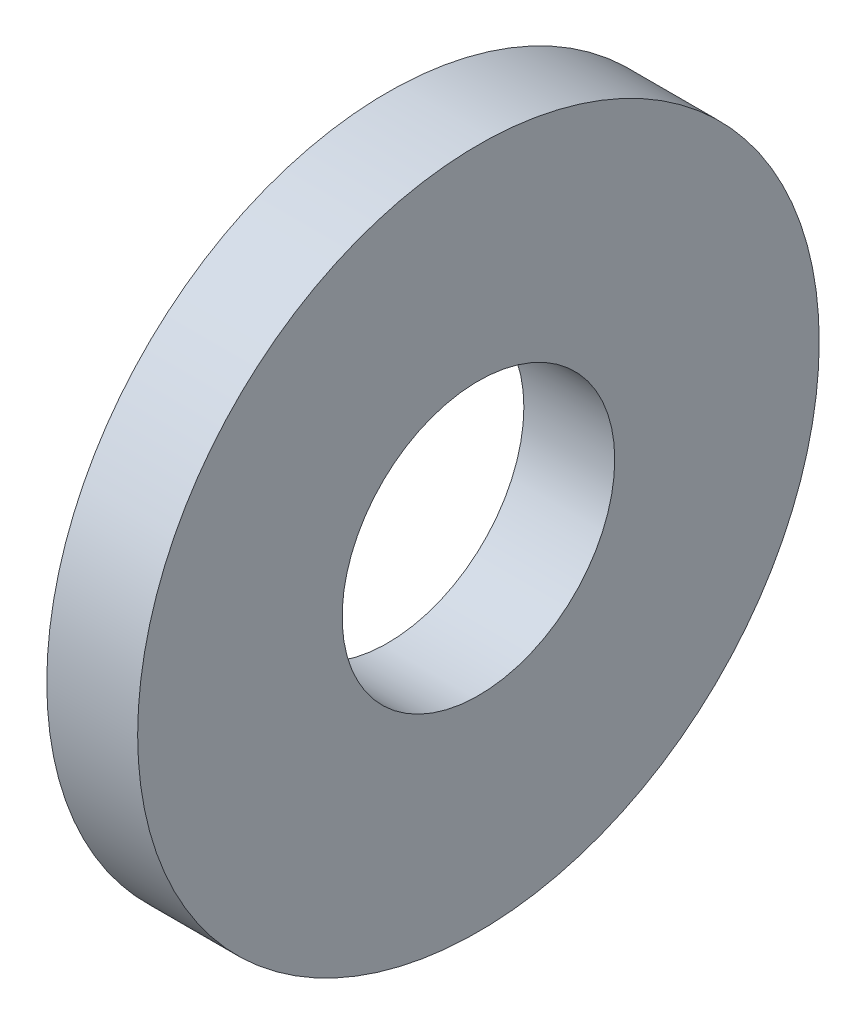
SolidWorks part; units mm, degrees
material "Acrylic (Medium-high impact)"
ref_plane "Front Plane" through (0, 0, 0) normal (0, 0, 1) x (1, 0, 0)
ref_plane "Top Plane" through (0, 0, 0) normal (0, 1, 0) x (1, 0, 0)
ref_plane "Right Plane" through (0, 0, 0) normal (1, 0, 0) x (0, 0, -1)
sketch "Sketch1" plane through (0, 0, 0) normal (1, 0, 0) x (0, 0, -1)
  circle A0 centre (0, 0) radius 7.5
  dimension "D1" = 15
extrude "Boss-Extrude1" add sketch "Sketch1" along normal blind 2
sketch "Sketch2" plane through (2, 0, 0) normal (1, 0, 0) x (0, 0, -1)
  circle A0 centre (0, 0) radius 3
  dimension "D1" = 6
extrude "Cut-Extrude1" cut sketch "Sketch2" against normal through all and the other way through all
